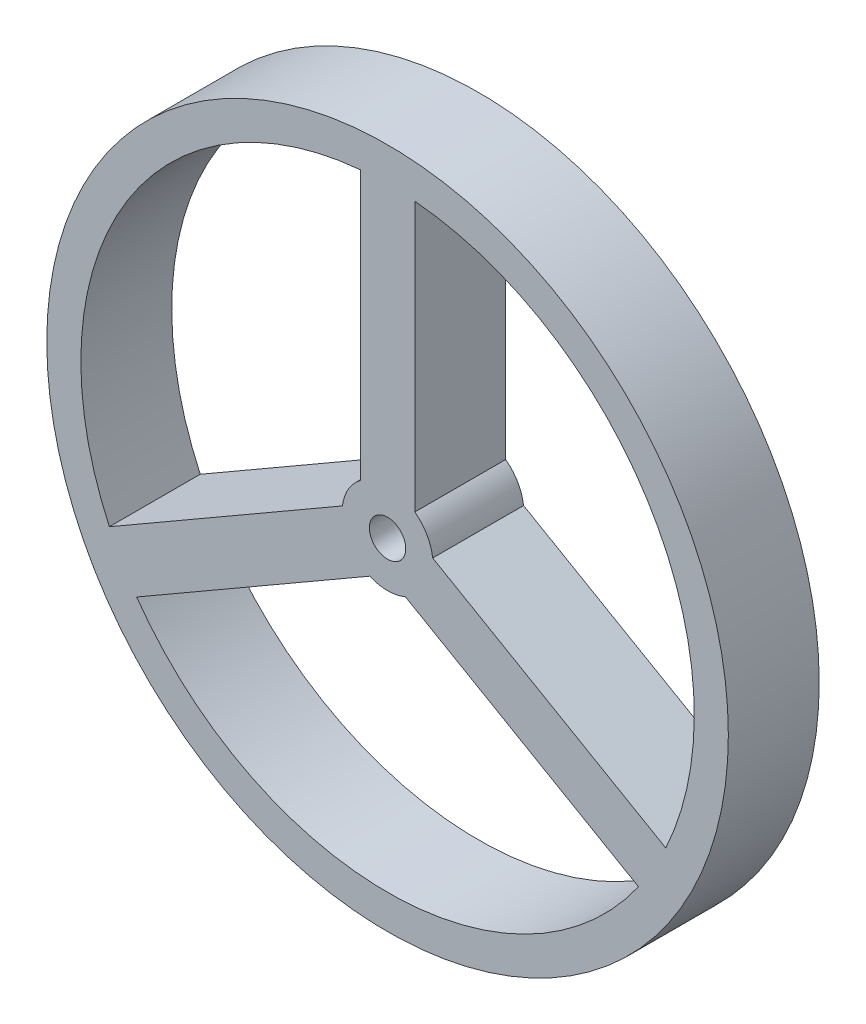
SolidWorks part; units mm, degrees
material "ABS"
ref_plane "前视基准面" through (0, 0, 0) normal (0, 0, 1) x (1, 0, 0)
ref_plane "上视基准面" through (0, 0, 0) normal (0, 1, 0) x (1, 0, 0)
ref_plane "右视基准面" through (0, 0, 0) normal (1, 0, 0) x (0, 0, -1)
sketch "Sketch1" plane through (0, 0, 0) normal (0, 0, 1) x (1, 0, 0)
  line L0 (0, 0) -> (0, 6.75) construction
  line L1 (0.6, 0.8) -> (0.6, 6.75)
  line L2 (-0.6, 0.8) -> (-0.6, 6.75)
  line L3 (0.9928, 0.1196) -> (6.1457, -2.8554)
  line L4 (0.3928, -0.9196) -> (5.5457, -3.8946)
  line L5 (-0.3928, -0.9196) -> (-5.5457, -3.8946)
  line L6 (-0.9928, 0.1196) -> (-6.1457, -2.8554)
  line L8 (-0.6, 0) -> (-0.6, 6.75) construction
  line L9 (0.6, 0) -> (0.6, 6.75) construction
  circle A4 centre (0, 0) radius 0.4
  circle A5 centre (0, 0) radius 1
  circle A6 centre (0, 0) radius 6.75
  circle A7 centre (0, 0) radius 7.5
  point P7 (0.6, 0)
  point P11 (0.6, 7.5)
  point P12 (-14, -0.6)
  point P13 (0, -0.6)
  point P14 (-0.75, 0)
  point P15 (-0.75, -7.5)
  point P17 (7.5187, -0.75)
  point P18 (-0.75, 0)
  point P19 (-0.75, 7.5187)
  point P20 (-14, 0.6)
  point P21 (0, 0.6)
  point P22 (0.6, 0)
  point P23 (0.6, -7.5)
  point P25 (14, 0.6)
  dimension "D1" = 15
  dimension "D2" = 13.5
  dimension "D3" = 0.6
  dimension "D4" = 0.6
  dimension "D6" = 0.8
  dimension "D7" = 2
  dimension "D5" = 3
extrude "Boss-Extrude1" add sketch "Sketch1" along normal blind 2
